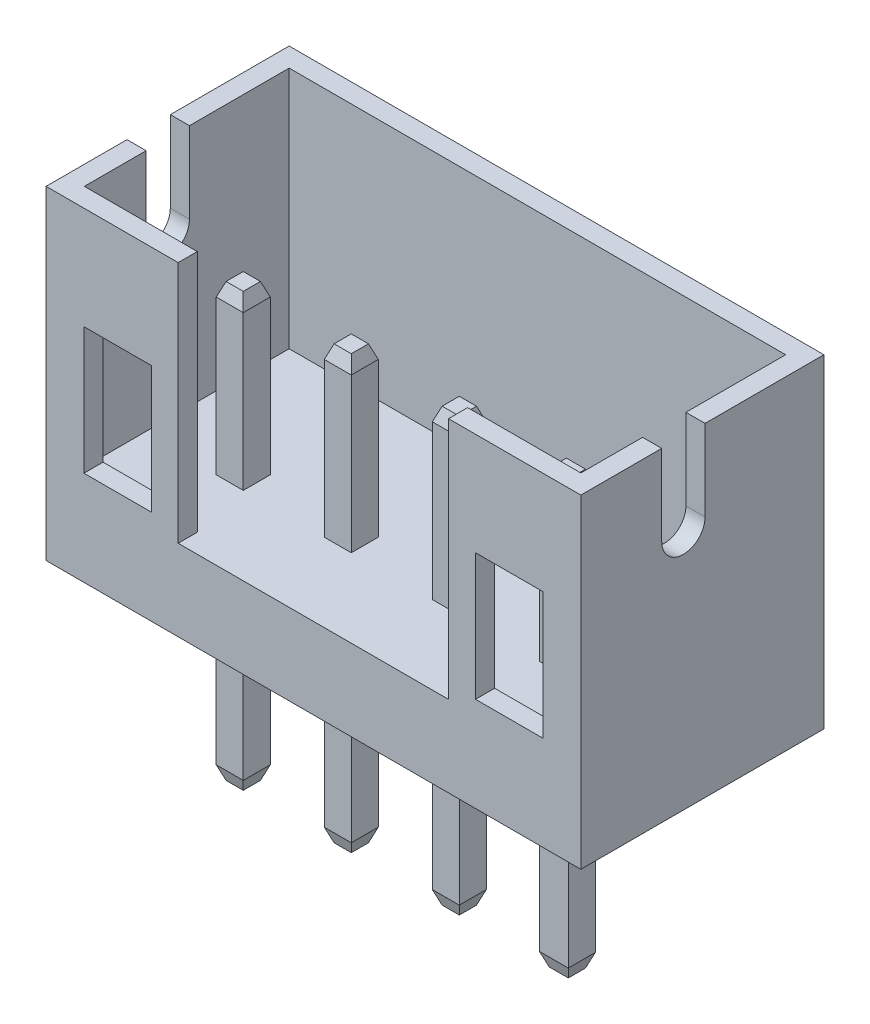
SolidWorks part; units mm, degrees
ref_plane "Front Plane" through (0, 0, 0) normal (0, 0, 1) x (1, 0, 0)
ref_plane "Top Plane" through (0, 0, 0) normal (0, 1, 0) x (1, 0, 0)
ref_plane "Right Plane" through (0, 0, 0) normal (1, 0, 0) x (0, 0, -1)
sketch "Sketch1" plane through (0, 0, 0) normal (0, 0, 1) x (1, 0, 0)
  line L1 (0, 0) -> (9.9, 0)
  line L2 (0, 0) -> (0, 6)
  line L3 (0, 6) -> (9.9, 6)
  line L4 (9.9, 0) -> (9.9, 6)
  point P5 (0, 0)
  point P6 (0, 0)
  point P7 (0, 0)
  dimension "D1" = 9.9
  dimension "D2" = 6
extrude "Boss-Extrude1" add sketch "Sketch1" against normal blind 4.5
sketch "Sketch2" plane through (0, 6, 0) normal (0, 1, 0) x (1, 0, 0)
  line L5 (9.5457, 0.3543) -> (0.3543, 0.3543)
  line L6 (9.5457, 0.3543) -> (9.5457, 4.1457)
  line L7 (9.5457, 4.1457) -> (0.3543, 4.1457)
  line L8 (0.3543, 0.3543) -> (0.3543, 4.1457)
  line L9 (9.5457, 0.3543) -> (0.3543, 4.1457) construction
  line L10 (9.5457, 4.1457) -> (0.3543, 0.3543) construction
  point P8 (4.95, 2.25)
extrude "Cut-Extrude1" cut sketch "Sketch2" against normal blind 4.5
sketch "Sketch3" plane through (0, 1.5, 0) normal (0, 1, 0) x (1, 0, 0)
  line L10 (2.4451, 0.3543) -> (7.45, 0.3543)
  line L11 (2.4451, 0.3543) -> (2.4451, 0)
  line L12 (2.4451, 0) -> (7.45, 0)
  line L13 (7.45, 0.3543) -> (7.45, 0)
extrude "Cut-Extrude2" cut sketch "Sketch3" along normal blind 4.5
sketch "Sketch5" plane through (9.9, 0, 0) normal (1, 0, 0) x (0, 0, -1)
  line L0 (1.4979, 6) -> (2.2995, 6)
  line L1 (4.5, 6) -> (0, 6) construction
  line L3 (1.4979, 6) -> (1.4979, 4.5)
  line L4 (1.4979, 4.5) -> (2.2995, 4.5)
  line L5 (2.2995, 4.5) -> (2.2995, 6)
  circle A0 centre (1.8987, 4.5) radius 0.4008
  line M5 (4.5, 6) -> (0, 6)
extrude "Cut-Extrude3" cut sketch "Sketch5" against normal blind 0.5 contours A0 L5 L3 M5 | L4 A0 | L4 A0
ref_plane "Plane1" through (4.95, 0, 0) normal (1, 0, 0) x (0, 0, -1)
mirror "Mirror1" about plane through (4.95, 0, 0) normal (1, 0, 0) of "Cut-Extrude3"
sketch "Sketch6" plane through (0, 0, 0) normal (0, 0, 1) x (1, 0, 0)
  line L0 (0, 0) -> (9.9, 0)
  line L1 (4.95, 0) -> (4.95, 1.5)
  line L2 (9.5457, 1.5) -> (0.3543, 1.5) construction
  line L3 (4.95, 1.5) -> (4.95, 1.7507)
  line L4 (4.95, -2.475) -> (4.95, 2.475) construction
  line L7 (1.9502, 1.7507) -> (0.7002, 1.7507)
  line L8 (1.9502, 1.7507) -> (1.9502, 4.1007)
  line L9 (1.9502, 4.1007) -> (0.7002, 4.1007)
  line L10 (0.7002, 1.7507) -> (0.7002, 4.1007)
  line L11 (7.95, 1.7507) -> (9.2, 1.7507)
  line L12 (7.95, 1.7507) -> (7.95, 4.1007)
  line L13 (7.95, 4.1007) -> (9.2, 4.1007)
  line L14 (9.2, 1.7507) -> (9.2, 4.1007)
  dimension "D1" = 1.25
  dimension "D2" = 2.35
  dimension "D3" = 1.25
extrude "Cut-Extrude4" cut sketch "Sketch6" against normal blind 0.5 contours L10 L7 L8 L9 | L11 L14 L13 L12
sketch "Sketch10" plane through (0, 0, 0) normal (0, 1, 0) x (1, 0, 0)
  line L1 (1.7, 1.95) -> (2.2, 1.95)
  line L2 (1.7, 1.95) -> (1.7, 1.45)
  line L3 (1.7, 1.45) -> (2.2, 1.45)
  line L4 (2.2, 1.95) -> (2.2, 1.45)
  line L7 (3.7, 1.45) -> (4.2, 1.45)
  line L8 (3.7, 1.45) -> (3.7, 1.95)
  line L9 (3.7, 1.95) -> (4.2, 1.95)
  line L10 (4.2, 1.45) -> (4.2, 1.95)
  line L13 (5.7, 1.95) -> (6.2, 1.95)
  line L14 (5.7, 1.95) -> (5.7, 1.45)
  line L15 (5.7, 1.45) -> (6.2, 1.45)
  line L16 (6.2, 1.95) -> (6.2, 1.45)
  line L19 (7.6822, 1.95) -> (8.2178, 1.95)
  line L20 (7.6822, 1.95) -> (7.6822, 1.45)
  line L21 (7.6822, 1.45) -> (8.2178, 1.45)
  line L22 (8.2178, 1.95) -> (8.2178, 1.45)
  point P6 (0, 0)
  point P12 (0, 0)
  point P18 (0, 0)
  point P24 (0, 0)
  point P25 (0, 0)
  point P26 (0, 0)
  point P27 (0, 0)
extrude "Boss-Extrude3" add sketch "Sketch10" along normal blind 8 from offset 3.4 offset against normal yes
chamfer "Chamfer1" distance 0.25 angle 20 4 edges at (1.95, 4.6, -1.45) (1.7, 4.6, -1.7) (1.95, 4.6, -1.95) (2.2, 4.6, -1.7)
chamfer "Chamfer2" distance 0.25 angle 20 12 edges at (3.95, 4.6, -1.45) (3.7, 4.6, -1.7) (3.95, 4.6, -1.95) (4.2, 4.6, -1.7) (5.95, 4.6, -1.45) (5.7, 4.6, -1.7) (5.95, 4.6, -1.95) (6.2, 4.6, -1.7) (7.95, 4.6, -1.45) (7.6822, 4.6, -1.7) (7.95, 4.6, -1.95) (8.2178, 4.6, -1.7)
chamfer "Chamfer3" distance 0.25 angle 20 16 edges at (1.95, -3.4, -1.95) (1.7, -3.4, -1.7) (1.95, -3.4, -1.45) (2.2, -3.4, -1.7) (7.95, -3.4, -1.95) (7.6822, -3.4, -1.7) (7.95, -3.4, -1.45) (8.2178, -3.4, -1.7) (5.95, -3.4, -1.95) (5.7, -3.4, -1.7) (5.95, -3.4, -1.45) (6.2, -3.4, -1.7) (3.95, -3.4, -1.95) (3.7, -3.4, -1.7) (3.95, -3.4, -1.45) (4.2, -3.4, -1.7)
